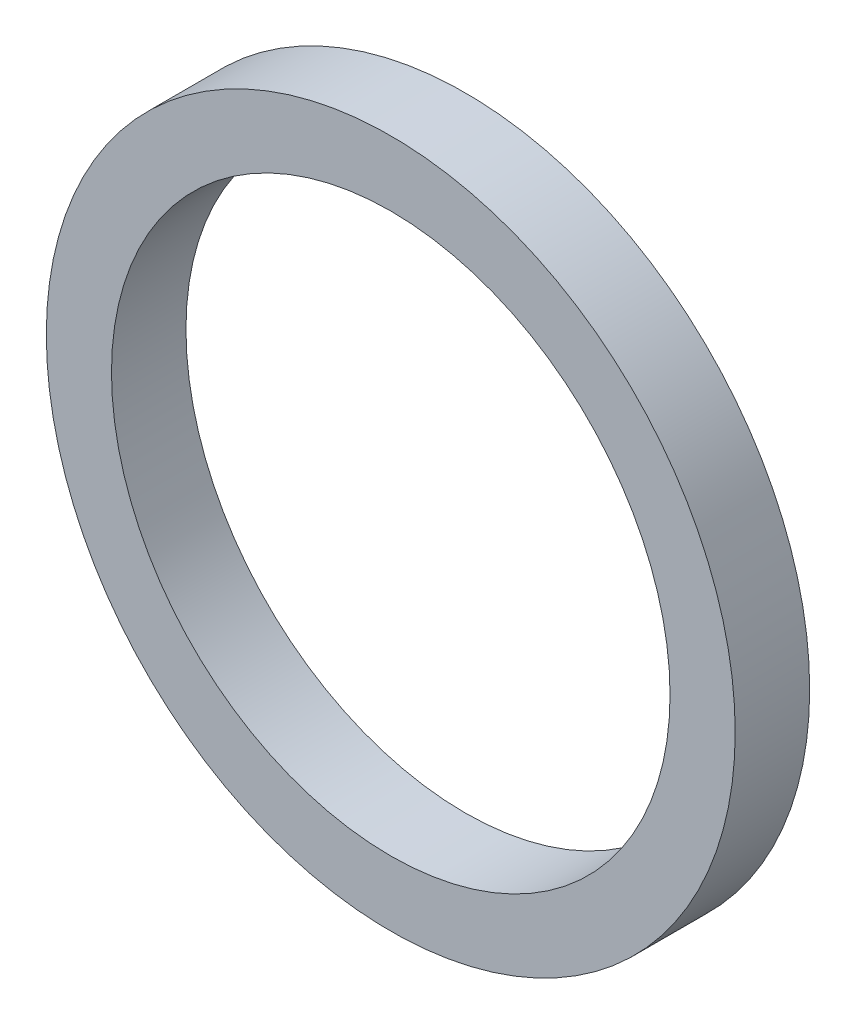
SolidWorks part; units mm, degrees
ref_plane "前视基准面" through (0, 0, 0) normal (0, 0, 1) x (1, 0, 0)
ref_plane "上视基准面" through (0, 0, 0) normal (0, 1, 0) x (1, 0, 0)
ref_plane "右视基准面" through (0, 0, 0) normal (1, 0, 0) x (0, 0, -1)
sketch "草图1" plane through (0, 0, 0) normal (0, 0, 1) x (1, 0, 0)
  circle A0 centre (0, 0) radius 15
  circle A1 centre (0, 0) radius 18.5
  dimension "D1" = 30
  dimension "D2" = 37
extrude "凸台-拉伸1" add sketch "草图1" along normal blind 4
